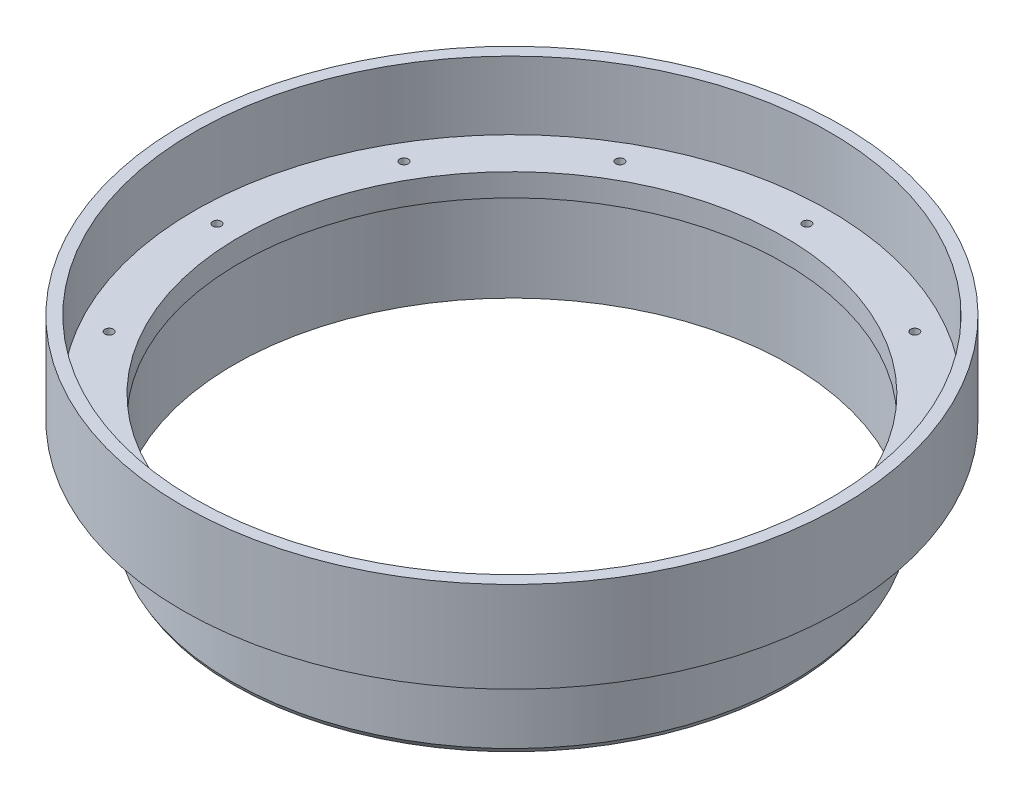
SolidWorks part; units mm, degrees
material "6061-T6 (SS)"
ref_plane "Front Plane" through (0, 0, 0) normal (0, 0, 1) x (1, 0, 0)
ref_plane "Top Plane" through (0, 0, 0) normal (0, 1, 0) x (1, 0, 0)
ref_plane "Right Plane" through (0, 0, 0) normal (1, 0, 0) x (0, 0, -1)
ref_axis "Axis1" through (0, 55, 0) along (0, -1, 0)
sketch "Cross Section" plane through (0, 0, 0) normal (0, 0, 1) x (1, 0, 0)
  line L0 (-38.1, 0) -> (-38.1, -3.175)
  line L1 (-38.1, -3.175) -> (-38.8874, -3.175)
  line L2 (-38.8874, -3.175) -> (-38.8874, -15.875)
  line L3 (-38.8874, -15.875) -> (-39.2684, -15.2151)
  line L4 (0, -15.875) -> (-38.1, -15.875) construction
  line L5 (-39.2684, -15.2151) -> (-39.2684, -3.175)
  line L6 (-39.2684, -3.175) -> (-46.1264, -3.175)
  line L7 (-46.1264, -3.175) -> (-46.1264, 9.525)
  line L8 (-46.1264, 9.525) -> (-44.45, 9.525)
  line L9 (-44.45, 9.525) -> (-44.45, 0)
  line L10 (-44.45, 0) -> (-38.1, 0)
  line L11 (-38.1, 0) -> (0, 0) construction
  line L12 (0, 55) -> (0, -55) construction
  line L14 (-44.45, 1.5875) -> (-44.45, 3.175) construction
  dimension "D1" = 0.7874
  dimension "D3" = 0.381
  dimension "D4" = 30
  dimension "D5" = 6.858
  dimension "D6" = 12.7
  dimension "D9" = 3.175
  dimension "D8" = 38.1
revolve "Main" add sketch "Cross Section" angle 360 about axis through (0, 55, 0) along (0, -1, 0)
sketch "Hole Location" plane through (0, 0, 0) normal (0, 1, 0) x (1, 0, 0)
  line L0 (0, 0) -> (-41.275, 0) construction
  circle A0 centre (0, 0) radius 41.275 construction
  dimension "D1" = 82.55
hole_wizard "#0-80 Tapped Hole1" positions "Sketch5" profile "Sketch7" tap size "#0-80" standard "ANSI Inch"
sketch "Sketch5" plane through (0, 0, 0) normal (0, 1, 0) x (1, 0, 0)
  point P0 (-41.275, 0)
sketch "Sketch7" plane through (-41.275, 0, 0) normal (1, 0, 0) x (0, 0, 1)
  line L0 (0, 0) -> (0, 3.5329)
  line L1 (0, 3.5329) -> (0.5956, 3.175)
  line L2 (0.5956, 3.175) -> (0.5956, 0)
  line L5 (0.5956, 0) -> (0, 0)
  line L10 (0, 3.5329) -> (-0.5956, 3.175) construction
  line L11 (0, -6.35) -> (0, 107.95) construction
  dimension "Tap Drill Dia." = 1.1913
  dimension "Tap Drill Depth" = 3.175
  dimension "Drill Angle" = 118
cosmetic thread "Hole Thread1" parameters "D1"=3.048, "D2"=1.524
pattern_circular "Screw Holes" count 12 over 360 about axis through (0, 0, 0) along (0, 1, 0) of "#0-80 Tapped Hole1"
equation "\"D8@Cross Section\"=\"TANK DIAMETER@Cryo Tank.Assembly\"/2"
equation "\"D1@Hole Location\"=\"TANK DIAMETER@Cryo Tank.Assembly\"+\"GASKET SEAT THICKNESS@Cryo Tank.Assembly\""
equation "\"D1@Cross Section\"=\"LINER THICKNESS@Cryo Tank.Assembly\""
equation "\"D3@Cross Section\"=\"ALUMINUM LAP THICKNESS@Cryo Tank.Assembly\""
equation "\"D5@Cross Section\"=2*\"CF THICKNESS@Cryo Tank.Assembly\"+\"NOMEX THICKNESS@Cryo Tank.Assembly\""
